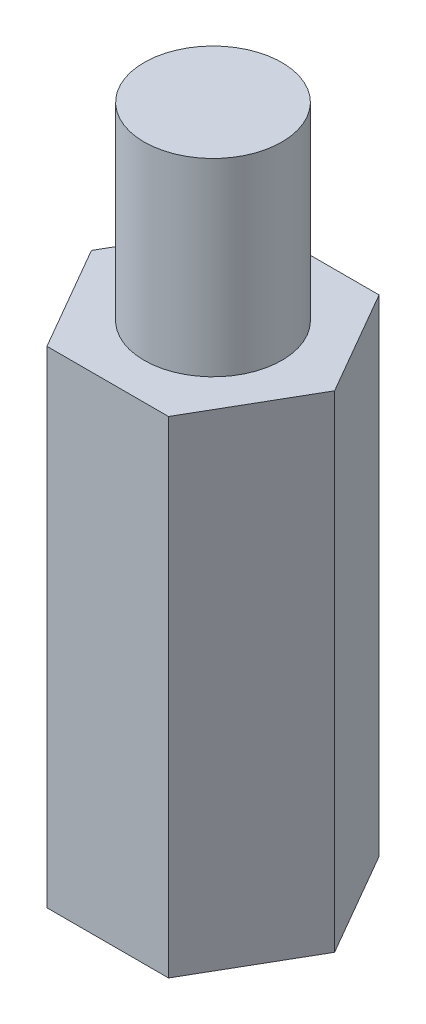
SolidWorks part; units mm, degrees
ref_plane "前视基准面" through (0, 0, 0) normal (0, 0, 1) x (1, 0, 0)
ref_plane "上视基准面" through (0, 0, 0) normal (0, 1, 0) x (1, 0, 0)
ref_plane "右视基准面" through (0, 0, 0) normal (1, 0, 0) x (0, 0, -1)
sketch "草图1" plane through (0, 0, 0) normal (0, 1, 0) x (1, 0, 0)
  line L1 (4.5, 0) -> (2.25, 3.8971)
  line L2 (2.25, 3.8971) -> (-2.25, 3.8971)
  line L3 (-2.25, 3.8971) -> (-4.5, 0)
  line L4 (-4.5, 0) -> (-2.25, -3.8971)
  line L5 (-2.25, -3.8971) -> (2.25, -3.8971)
  line L6 (2.25, -3.8971) -> (4.5, 0)
  circle A0 centre (0, 0) radius 2.5
  circle A1 centre (0, 0) radius 3.8971 construction
  dimension "D1" = 5
  dimension "D2" = 9
extrude "凸台-拉伸1" add sketch "草图1" along normal blind 18
ref_plane "基准面1" through (0, 18, 0) normal (0, 1, 0) x (1, 0, 0)
sketch "草图2" plane through (0, 18, 0) normal (0, 1, 0) x (1, 0, 0)
  circle A0 centre (0, 0) radius 2.55
  dimension "D1" = 5.1
extrude "凸台-拉伸2" add sketch "草图2" along normal blind 7
